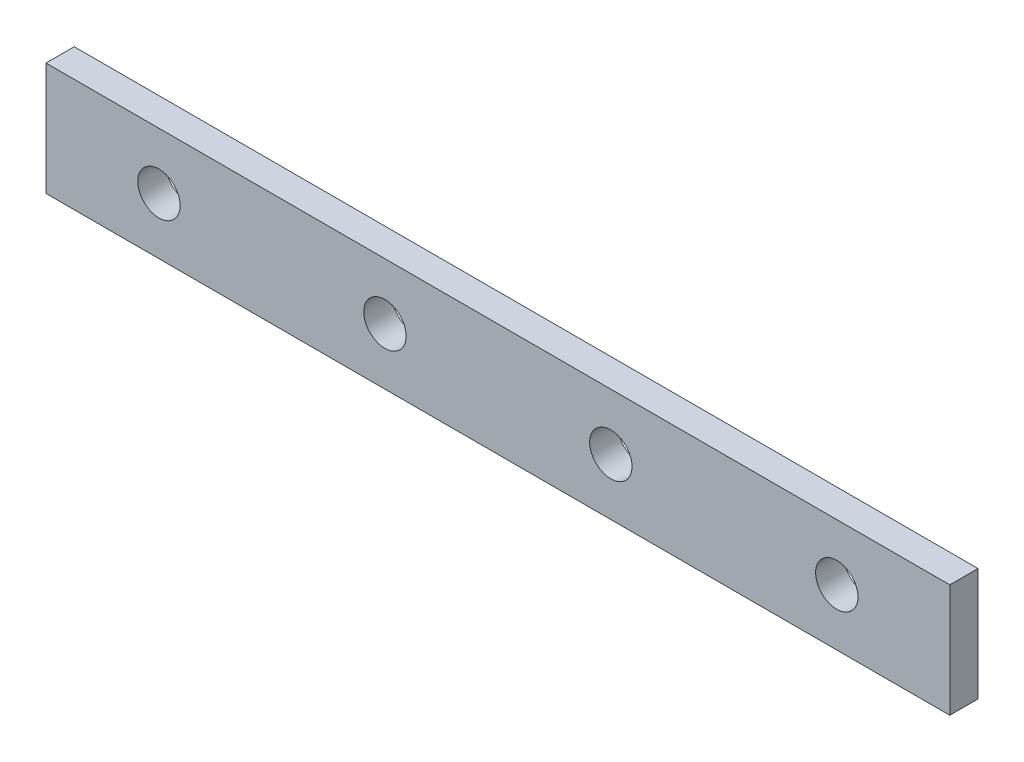
SolidWorks part; units mm, degrees
ref_plane "Front Plane" through (0, 0, 0) normal (0, 0, 1) x (1, 0, 0)
ref_plane "Top Plane" through (0, 0, 0) normal (0, 1, 0) x (1, 0, 0)
ref_plane "Right Plane" through (0, 0, 0) normal (1, 0, 0) x (0, 0, -1)
sketch "Sketch1" plane through (0, 0, 0) normal (0, 0, 1) x (1, 0, 0)
  line L1 (101.6, -12.7) -> (-101.6, -12.7)
  line L2 (101.6, -12.7) -> (101.6, 12.7)
  line L3 (101.6, 12.7) -> (-101.6, 12.7)
  line L4 (-101.6, -12.7) -> (-101.6, 12.7)
  line L5 (101.6, -12.7) -> (-101.6, 12.7) construction
  line L6 (101.6, 12.7) -> (-101.6, -12.7) construction
  point P0 (0, 0)
  dimension "D1" = 25.4
  dimension "D2" = 203.2
extrude "Boss-Extrude1" add sketch "Sketch1" along normal blind 6.35
sketch "Sketch2" plane through (0, 0, 6.35) normal (0, 0, 1) x (1, 0, 0)
  line L0 (-101.6, 0) -> (-76.2, 0) construction
  line L1 (-101.6, 12.7) -> (-101.6, -12.7) construction
  circle A0 centre (-76.2, 0) radius 4.7625
  point P5 (-101.6, 0)
  dimension "D1" = 25.4
  dimension "D2" = 9.525
  dimension "D3" = 0
extrude "Cut-Extrude1" cut sketch "Sketch2" against normal through all contours A0
pattern_linear "LPattern1" count 4 spacing 50.8 along (1, 0, 0) of "Cut-Extrude1"
equation "\"NumHoles\"= \"D2@Sketch1\" / 2"
equation "\"D1@LPattern1\"= \"NumHoles\""
equation "\"TotalLength\" = \"D2@Sketch1\""
equation "\"D1@Sketch2\"= ( \"TotalLength\" - ( \"D1@LPattern1\" - 1 ) * 2 ) / 2"
